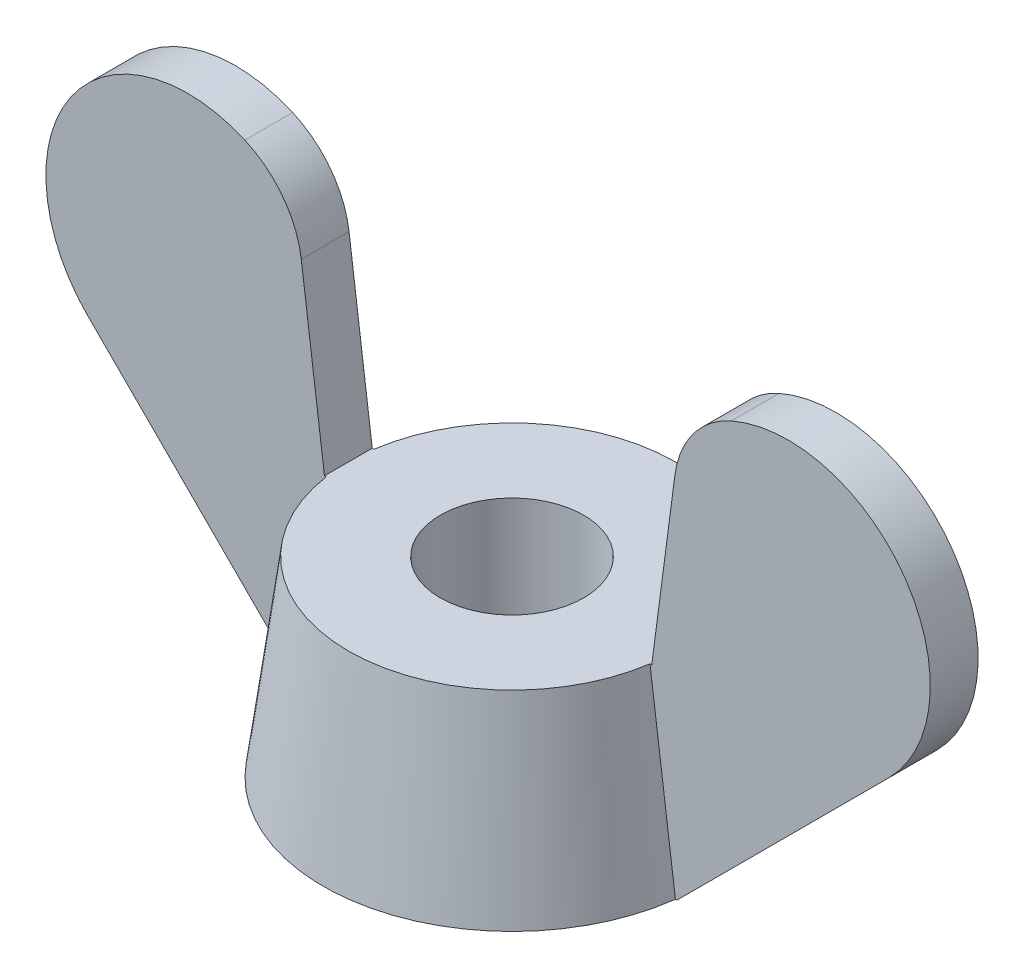
SolidWorks part; units mm, degrees
ref_plane "前视基准面" through (0, 0, 0) normal (0, 0, 1) x (1, 0, 0)
ref_plane "上视基准面" through (0, 0, 0) normal (0, 1, 0) x (1, 0, 0)
ref_plane "右视基准面" through (0, 0, 0) normal (1, 0, 0) x (0, 0, -1)
sketch "草图1" plane through (0, 0, 0) normal (0, 1, 0) x (1, 0, 0)
  circle A0 centre (0, 0) radius 3.95
  dimension "D1" = 7.9
extrude "凸台-拉伸1" add sketch "草图1" along normal blind 4 draft 7.5 contours A0
sketch "草图2" plane through (0, 0, 0) normal (0, 1, 0) x (1, 0, 0)
  circle A0 centre (0, 0) radius 1.5
  dimension "D1" = 3
extrude "切除-拉伸1" cut sketch "草图2" along normal blind 4
sketch "草图3" plane through (0, 0, 0) normal (0, 0, 1) x (1, 0, 0)
  line L0 (0, 0) -> (0, 9.5) construction
  line L1 (-3.95, 0) -> (3.95, 0) construction
  line L2 (0, 9.5) -> (9.25, 9.5) construction
  line L3 (9.25, 9.5) -> (9.25, 0) construction
  line L4 (9.25, 0) -> (0, 0) construction
  line L5 (3.95, 0) -> (9.25, 5.3) construction
  line L6 (3.95, 0) -> (3.4234, 4) construction
  line L7 (3.4234, 4) -> (4.1475, 9.5) construction
  line L8 (8.3802, 4.4302) -> (3.95, 0)
  line L9 (3.9078, 7.6794) -> (3.4234, 4)
  line L14 (3.4234, 4) -> (1.95, 4)
  line L15 (3.4234, 4) -> (-3.4234, 4) construction
  line L16 (1.95, 4) -> (1.95, 0)
  line L17 (1.95, 0) -> (3.95, 0)
  line L18 (-1.95, 4) -> (-1.95, 0)
  line L19 (-3.4234, 4) -> (-1.95, 4)
  line L20 (-3.9078, 7.6794) -> (-3.4234, 4)
  line L21 (-8.3802, 4.4302) -> (-3.95, 0)
  line L22 (-1.95, 0) -> (-3.95, 0)
  arc A0 (5.0875, 9.25) -> (8.3802, 4.4302) centre (6.2802, 6.5302) cw
  arc A1 (3.9078, 7.6794) -> (5.0875, 9.25) centre (5.8907, 7.4184) cw
  arc A2 (-3.9078, 7.6794) -> (-5.0875, 9.25) centre (-5.8907, 7.4184) ccw
  arc A3 (-5.0875, 9.25) -> (-8.3802, 4.4302) centre (-6.2802, 6.5302) ccw
  point P18 (4.0083, 8.4429)
  dimension "D5" = 2
  dimension "D1" = 9.25
  dimension "D2" = 9.5
  dimension "D3" = 45
  dimension "D4" = 7.5
  dimension "D6" = 2
extrude "凸台-拉伸2" add sketch "草图3" along normal mid plane 1
